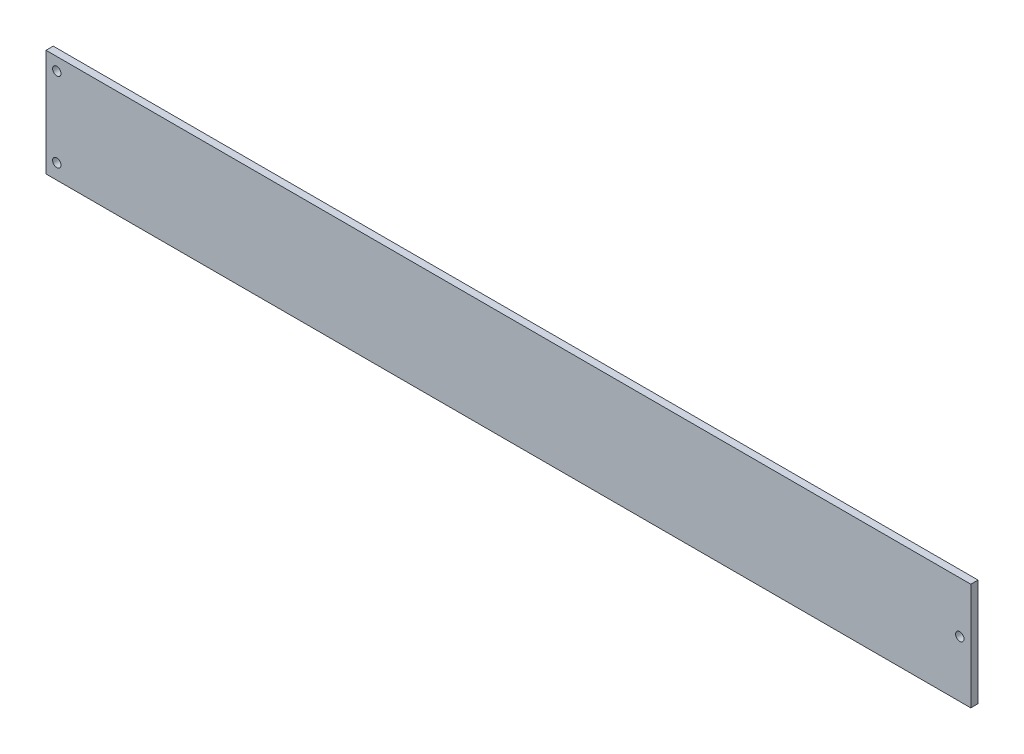
SolidWorks part; units mm, degrees
material "Verre"
ref_plane "Plan de face" through (0, 0, 0) normal (0, 0, 1) x (1, 0, 0)
ref_plane "Plan de dessus" through (0, 0, 0) normal (0, 1, 0) x (1, 0, 0)
ref_plane "Plan de droite" through (0, 0, 0) normal (1, 0, 0) x (0, 0, -1)
sketch "Esquisse1" plane through (0, 0, 0) normal (0, 0, 1) x (1, 0, 0)
  line L1 (-192.5, -22.3) -> (192.5, -22.3)
  line L2 (-192.5, -22.3) -> (-192.5, 22.3)
  line L3 (-192.5, 22.3) -> (192.5, 22.3)
  line L4 (192.5, -22.3) -> (192.5, 22.3)
  line L5 (-192.5, -22.3) -> (192.5, 22.3) construction
  line L6 (-192.5, 22.3) -> (192.5, -22.3) construction
  point P0 (0, 0)
  dimension "D1" = 44.6
  dimension "D2" = 385
extrude "Boss.-Extru.1" add sketch "Esquisse1" along normal blind 3
sketch "Esquisse3" plane through (0, 0, 3) normal (0, 0, 1) x (1, 0, 0)
  circle A0 centre (-188.0066, 17.0303) radius 1.75
  circle A1 centre (-188.0066, -15.9897) radius 1.75
  circle A2 centre (187.9134, 1.1553) radius 1.75
extrude "Enlèv. mat.-Extru.1" cut sketch "Esquisse3" against normal blind 10
